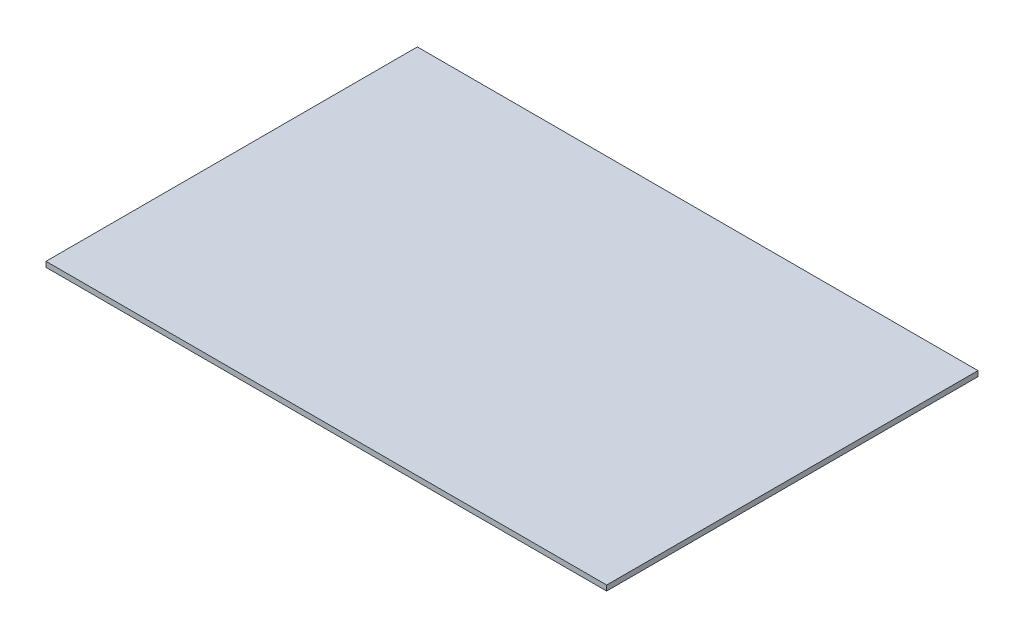
SolidWorks part; units mm, degrees
ref_plane "Front Plane" through (0, 0, 0) normal (0, 0, 1) x (1, 0, 0)
ref_plane "Top Plane" through (0, 0, 0) normal (0, 1, 0) x (1, 0, 0)
ref_plane "Right Plane" through (0, 0, 0) normal (1, 0, 0) x (0, 0, -1)
sketch "Sketch1" plane through (0, 0, 0) normal (0, 1, 0) x (1, 0, 0)
  line L1 (-84.4, 55.9) -> (84.4, 55.9)
  line L2 (-84.4, 55.9) -> (-84.4, -55.9)
  line L3 (-84.4, -55.9) -> (84.4, -55.9)
  line L4 (84.4, 55.9) -> (84.4, -55.9)
  line L5 (-84.4, 55.9) -> (84.4, -55.9) construction
  line L6 (-84.4, -55.9) -> (84.4, 55.9) construction
  point P0 (0, 0)
  dimension "D1" = 168.8
  dimension "D2" = 111.8
extrude "Boss-Extrude1" add sketch "Sketch1" along normal blind 1.5875
